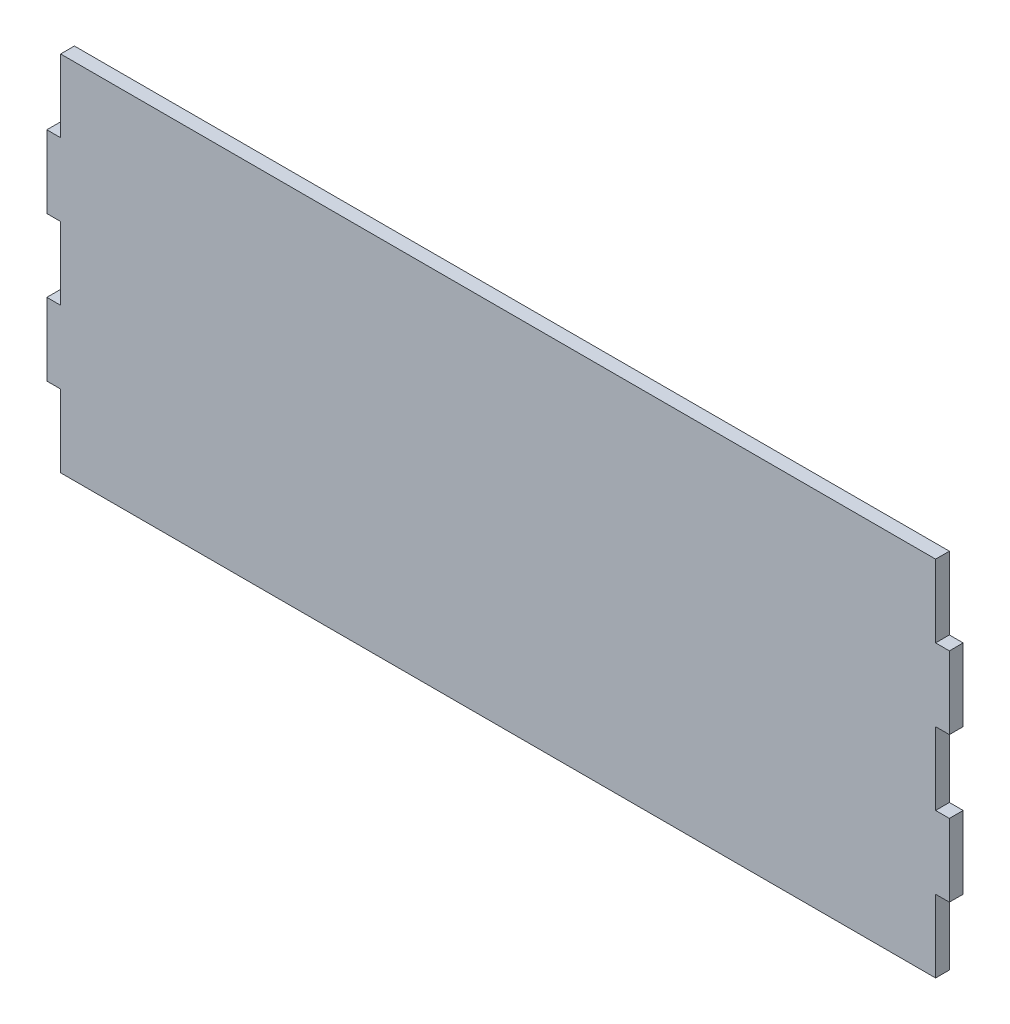
SolidWorks part; units mm, degrees
material "1060 Alloy"
ref_plane "Front Plane" through (0, 0, 0) normal (0, 0, 1) x (1, 0, 0)
ref_plane "Top Plane" through (0, 0, 0) normal (0, 1, 0) x (1, 0, 0)
ref_plane "Right Plane" through (0, 0, 0) normal (1, 0, 0) x (0, 0, -1)
sketch "Sketch1" plane through (0, 0, 0) normal (0, 0, 1) x (1, 0, 0)
  line L0 (0, 76.2) -> (0, 101.6)
  line L1 (4.826, 0) -> (311.15, 0)
  line L2 (0, 25.4) -> (0, 50.8)
  line L3 (4.826, 127) -> (311.15, 127)
  line L4 (311.15, 0) -> (311.15, 25.4)
  line L5 (311.15, 101.6) -> (315.976, 101.6)
  line L7 (311.15, 76.2) -> (315.976, 76.2)
  line L8 (315.976, 101.6) -> (315.976, 76.2)
  line L9 (311.15, 50.8) -> (315.976, 50.8)
  line L11 (311.15, 25.4) -> (315.976, 25.4)
  line L12 (315.976, 50.8) -> (315.976, 25.4)
  line L13 (311.15, 101.6) -> (311.15, 127)
  line L14 (311.15, 50.8) -> (311.15, 76.2)
  line L15 (0, 101.6) -> (4.826, 101.6)
  line L16 (4.826, 127) -> (4.826, 101.6)
  line L17 (0, 76.2) -> (4.826, 76.2)
  line L19 (0, 50.8) -> (4.826, 50.8)
  line L20 (4.826, 76.2) -> (4.826, 50.8)
  line L21 (0, 25.4) -> (4.826, 25.4)
  line L24 (4.826, 25.4) -> (4.826, 0)
  dimension "D1" = 127
  dimension "D2" = 311.15
  dimension "D4" = 4.826
extrude "Boss-Extrude1" add sketch "Sketch1" along normal blind 4.826 contours L3 L13 L5 L8 L7 L14 L9 L12 L11 L4 L1 L24 L21 L2 L19 L20 L17 L0 L15 L16
equation "\"w\"= .19"
equation "\"D4@Sketch1\"=\"w\""
equation "\"D1@Boss-Extrude1\"=\"w\""
